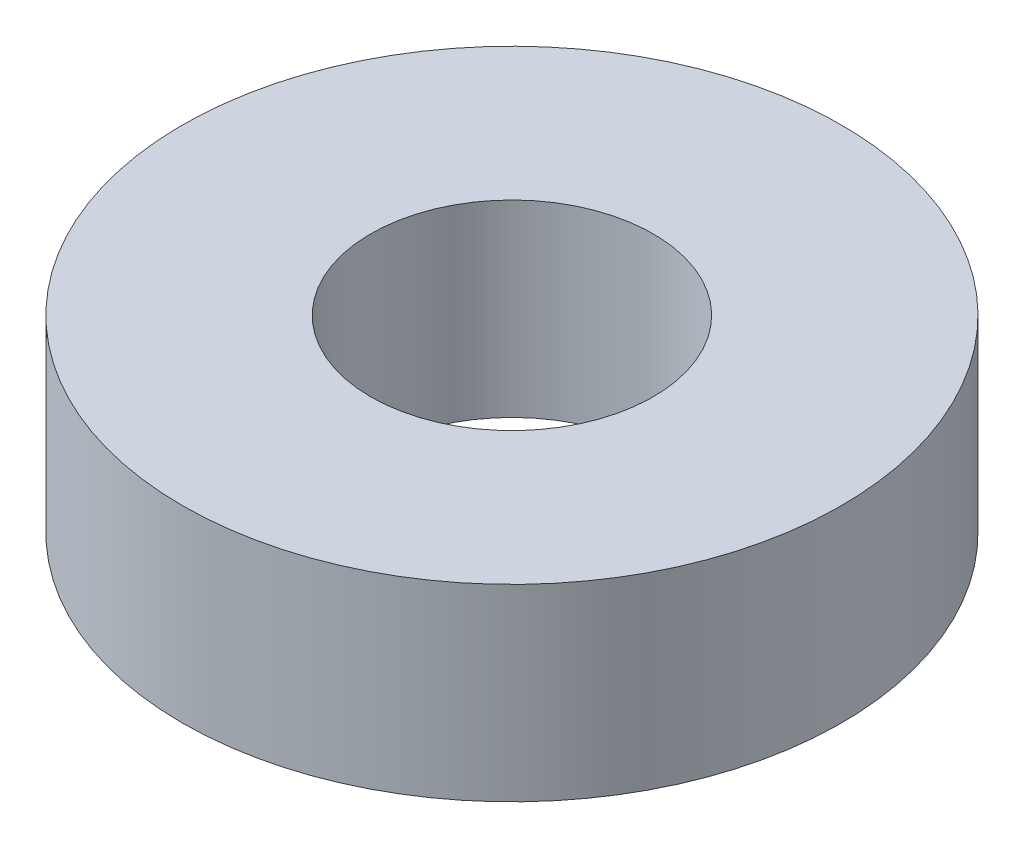
SolidWorks part; units mm, degrees
ref_plane "Front Plane" through (0, 0, 0) normal (0, 0, 1) x (1, 0, 0)
ref_plane "Top Plane" through (0, 0, 0) normal (0, 1, 0) x (1, 0, 0)
ref_plane "Right Plane" through (0, 0, 0) normal (1, 0, 0) x (0, 0, -1)
sketch "Sketch1" plane through (0, 0, 0) normal (0, 1, 0) x (1, 0, 0)
  circle A0 centre (0, 0) radius 14
  circle A1 centre (0, 0) radius 6
  dimension "D1" = 28
  dimension "D2" = 12
extrude "Boss-Extrude1" add sketch "Sketch1" along normal blind 8
